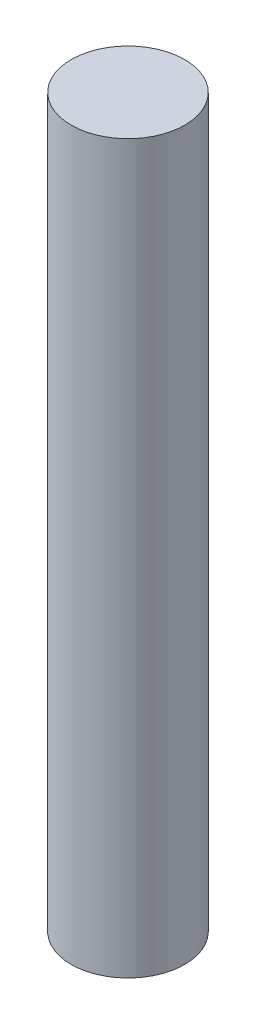
SolidWorks part; units mm, degrees
ref_plane "Front Plane" through (0, 0, 0) normal (0, 0, 1) x (1, 0, 0)
ref_plane "Top Plane" through (0, 0, 0) normal (0, 1, 0) x (1, 0, 0)
ref_plane "Right Plane" through (0, 0, 0) normal (1, 0, 0) x (0, 0, -1)
sketch "Sketch1" plane through (0, 0, 0) normal (0, 1, 0) x (1, 0, 0)
  circle A0 centre (0, 0) radius 3.175
  dimension "D1" = 6.35
extrude "Boss-Extrude1" add sketch "Sketch1" along normal blind 40.64
